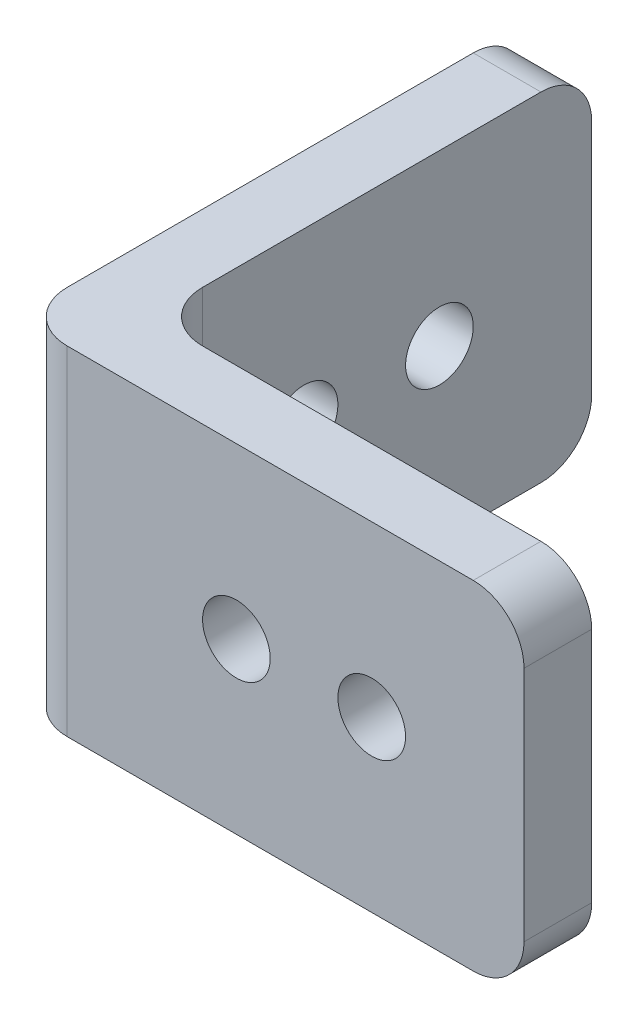
SolidWorks part; units mm, degrees
ref_plane "Front Plane" through (0, 0, 0) normal (0, 0, 1) x (1, 0, 0)
ref_plane "Top Plane" through (0, 0, 0) normal (0, 1, 0) x (1, 0, 0)
ref_plane "Right Plane" through (0, 0, 0) normal (1, 0, 0) x (0, 0, -1)
sketch "Sketch1" plane through (0, 0, 0) normal (0, 1, 0) x (1, 0, 0)
  line L0 (0, 0) -> (0, 30)
  line L1 (0, -55) -> (0, 55) construction
  line L2 (0, 30) -> (4, 30)
  line L3 (4, 30) -> (4, 4)
  line L4 (4, 4) -> (30, 4)
  line L5 (30, 4) -> (30, 0)
  line L6 (-55, 0) -> (55, 0) construction
  line L7 (30, 0) -> (0, 0)
  dimension "D1" = 30
extrude "Boss-Extrude1" add sketch "Sketch1" along normal blind 20
sketch "Sketch2" plane through (4, 0, 0) normal (1, 0, 0) x (0, 0, -1)
  line L0 (4, 10) -> (13, 10) construction
  line L1 (4, 20) -> (4, 0) construction
  line L2 (13, 10) -> (21, 10) construction
  circle A0 centre (13, 10) radius 2
  circle A1 centre (21, 10) radius 2
extrude "Cut-Extrude1" cut sketch "Sketch2" against normal through all
sketch "Sketch3" plane through (0, 0, -4) normal (0, 0, -1) x (-1, 0, 0)
  line L0 (-30, 10) -> (-21, 10) construction
  line L1 (-30, 20) -> (-30, 0) construction
  line L2 (-21, 10) -> (-13, 10) construction
  circle A0 centre (-21, 10) radius 2
  circle A1 centre (-13, 10) radius 2
extrude "Cut-Extrude2" cut sketch "Sketch3" against normal through all
fillet "Fillet1" radius 3 6 edges at (0, 10, 0) (2, 20, -30) (2, 0, -30) (4, 10, -4) (30, 0, -2) (30, 20, -2)
